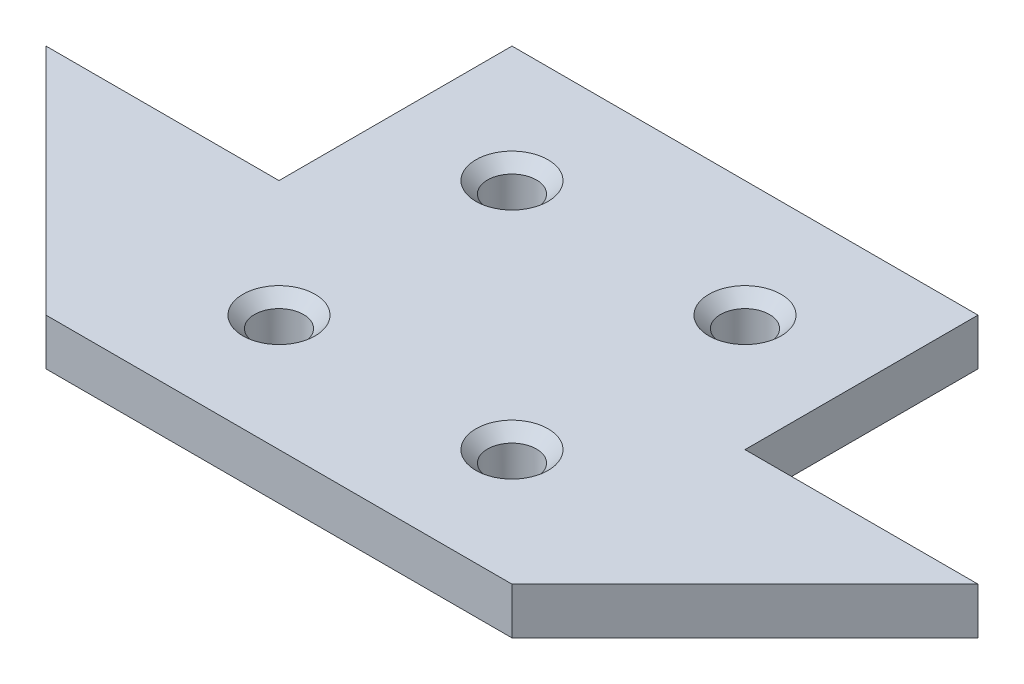
SolidWorks part; units mm, degrees
material "1060 Alloy"
ref_plane "Front Plane" through (0, 0, 0) normal (0, 0, 1) x (1, 0, 0)
ref_plane "Top Plane" through (0, 0, 0) normal (0, 1, 0) x (1, 0, 0)
ref_plane "Right Plane" through (0, 0, 0) normal (1, 0, 0) x (0, 0, -1)
sketch "Sketch1" plane through (0, 0, 0) normal (0, 1, 0) x (1, 0, 0)
  line L0 (-4.54, -33.2357) -> (35.46, -33.2357)
  line L1 (-4.54, 6.7643) -> (35.46, 6.7643)
  line L2 (-4.54, 6.7643) -> (-4.54, -13.2357)
  line L4 (35.46, 6.7643) -> (35.46, -13.2357)
  line L5 (35.46, -13.2357) -> (55.46, -13.2357)
  line L6 (55.46, -13.2357) -> (35.46, -33.2357)
  line L7 (15.46, 6.7643) -> (15.46, -33.2357) construction
  line L8 (-24.54, -13.2357) -> (-4.54, -33.2357)
  line L9 (-4.54, -13.2357) -> (-24.54, -13.2357)
  line L10 (-4.54, -13.2357) -> (-4.54, -33.2357)
  line L11 (35.46, -13.2357) -> (35.46, -33.2357)
  dimension "D1" = 40
  dimension "D2" = 40
  dimension "D3" = 20
extrude "Boss-Extrude1" add sketch "Sketch1" along normal blind 4 contours L1 L4 L5 L6 L0 L8 L9 L2
sketch "Sketch2" plane through (0, 4, 0) normal (0, 1, 0) x (1, 0, 0)
  line L0 (-4.54, -13.2357) -> (35.46, -13.2357) construction
  line L1 (35.46, -13.2357) -> (15.46, -33.2357) construction
  line L2 (15.46, -33.2357) -> (-4.54, -13.2357) construction
  circle A0 centre (5.46, -23.2357) radius 2.1
  circle A1 centre (25.46, -23.2357) radius 2.1
  circle A2 centre (25.46, -3.2357) radius 2.1
  circle A3 centre (5.46, -3.2357) radius 2.1
  dimension "D1" = 4.2
  dimension "D2" = 4.2
extrude "Cut-Extrude1" cut sketch "Sketch2" against normal blind 4
chamfer "Chamfer1" distance 1 angle 45 4 edges at (5.46, 4, 25.3357) (25.46, 4, 25.3357) (25.46, 4, 1.1357) (5.46, 4, 1.1357)
equation "\"tnut_length\"= 9.55"
equation "\"length\"= 40"
equation "\"height\"= 20"
equation "\"width\"= 4"
equation "\"hole_dia\"= 4.2"
equation "\"D1@Sketch1\"=\"length\""
equation "\"D2@Sketch1\"=\"height\"*2"
equation "\"D3@Sketch1\"=\"height\""
equation "\"D1@Boss-Extrude1\"=\"width\""
equation "\"D1@Sketch2\"=\"hole_dia\""
equation "\"D2@Sketch2\"=\"hole_dia\""
equation "\"D1@Cut-Extrude1\"=\"width\""
